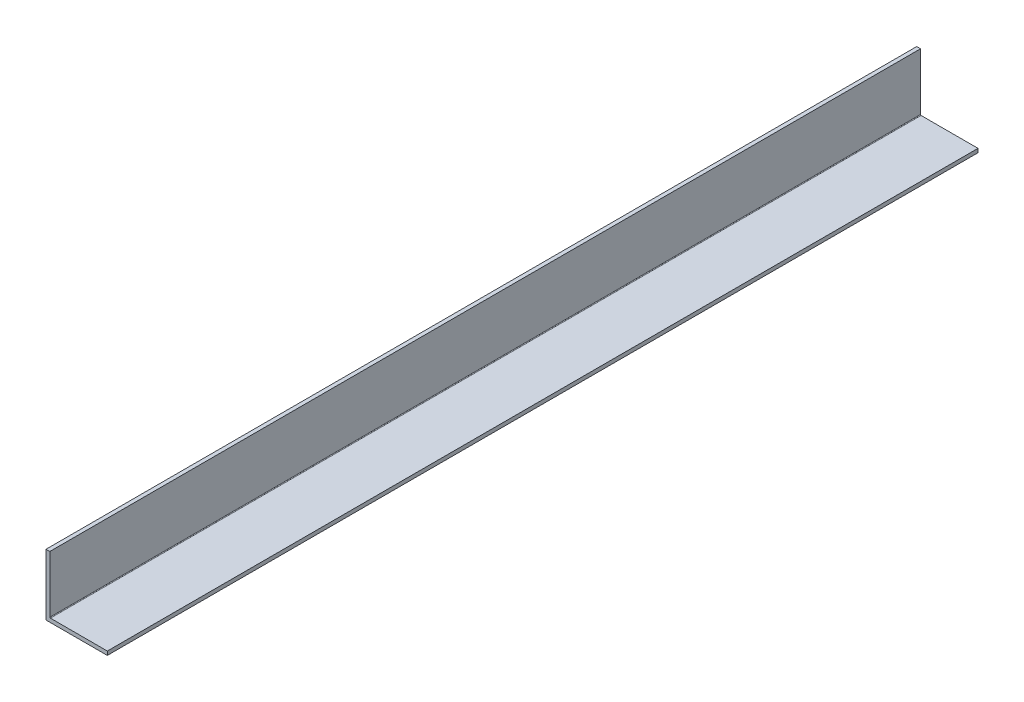
SolidWorks part; units mm, degrees
material "6061-T6 (SS)"
ref_plane "Front Plane" through (0, 0, 0) normal (0, 0, 1) x (1, 0, 0)
ref_plane "Top Plane" through (0, 0, 0) normal (0, 1, 0) x (1, 0, 0)
ref_plane "Right Plane" through (0, 0, 0) normal (1, 0, 0) x (0, 0, -1)
sketch "Sketch1" plane through (0, 0, 0) normal (0, 0, 1) x (1, 0, 0)
  line L0 (0, 25.4) -> (0, 0) construction
  line L1 (0, 0) -> (25.4, 0) construction
  line L2 (25.4, 0) -> (25.4, 1.5875) construction
  line L3 (25.4, 1.5875) -> (1.5875, 1.5875) construction
  line L4 (1.5875, 1.5875) -> (1.5875, 25.4) construction
  line L6 (1.5875, 25.4) -> (0, 25.4) construction
  arc A0 (1.5875, 1.8415) -> (1.8415, 1.5875) centre (1.8415, 1.8415) ccw construction
  point P4 (0, 0)
  dimension "Inside Corner Radius" = 0.254
  dimension "Outside Height" = 25.4
  dimension "Inside Height" = 23.8125
  dimension "Outside Width" = 25.4
  dimension "Inside Width" = 23.8125
  dimension "Wall Thickness" = 1.5875
  dimension "Shape" = 90
sketch "Sketch2" plane through (0, 0, 0) normal (1, 0, 0) x (0, 0, -1)
  line L0 (304.8, 0) -> (-304.8, 0) construction
  line L1 (-304.8, 25.4) -> (-304.8, 0) construction
  line L2 (304.8, 25.4) -> (304.8, 0) construction
  point P0 (-275.59, 0)
  point P4 (0, 0)
  point P6 (275.59, 0)
  dimension "D1" = 29.21
  dimension "D2" = 29.21
  dimension "D3" = 25.4
  dimension "Length" = 609.6
sketch "Sketch3" plane through (0, 0, 0) normal (0, 0, 1) x (1, 0, 0)
  line L0 (1.5875, 25.4) -> (0, 25.4)
  line L1 (0, 25.4) -> (0, 0)
  line L2 (0, 0) -> (25.4, 0)
  line L3 (25.4, 0) -> (25.4, 1.5875)
  line L4 (25.4, 1.5875) -> (1.5875, 1.5875)
  line L5 (1.5875, 1.5875) -> (1.5875, 25.4)
extrude "Boss-Extrude1" add sketch "Sketch3" along normal mid plane 609.6
fillet "Fillet1" radius 0.254 1 edges at (1.5875, 1.5875, 0)
sketch "Sketch4" plane through (0, 0, -304.8) normal (0, 0, -1) x (-1, 0, 0)
  line L6 (-1.5875, 25.4) -> (-1.5875, 1.8415)
  line L7 (-1.8415, 1.5875) -> (-25.4, 1.5875)
  line L8 (-25.4, 1.5875) -> (-25.4, 0)
  line L9 (-25.4, 0) -> (0, 0)
  line L10 (0, 0) -> (0, 25.4)
  line L11 (0, 25.4) -> (-1.5875, 25.4)
  line L12 (-1.5875, 25.4) -> (-1.5875, 1.8415)
  line L13 (-1.8415, 1.5875) -> (-25.4, 1.5875)
  line L14 (-25.4, 1.5875) -> (-25.4, 0)
  line L15 (-25.4, 0) -> (0, 0)
  line L16 (0, 0) -> (0, 25.4)
  line L17 (0, 25.4) -> (-1.5875, 25.4)
  arc A1 (-1.8415, 1.5875) -> (-1.5875, 1.8415) centre (-1.8415, 1.8415) ccw
  arc A2 (-1.8415, 1.5875) -> (-1.5875, 1.8415) centre (-1.8415, 1.8415) ccw
  dimension "D1" = 0
extrude "Cut-Extrude1" cut sketch "Sketch4" against normal offset from surface (248.9375 mm away) 360.6625 up to face at (7.9663, 7.9663, 304.8)
equation "\"D1@Boss-Extrude1\"=\"Length@Sketch2\""
equation "\"D1@Sketch2\" = \"Outside Width@Sketch1\" * 1.15"
equation "\"D2@Sketch2\"=\"D1@Sketch2\""
equation "\"D1@Fillet1\"=\"Inside Corner Radius@Sketch1\""
equation "\"D3@Sketch2\"=\"Outside Height@Sketch1\""
